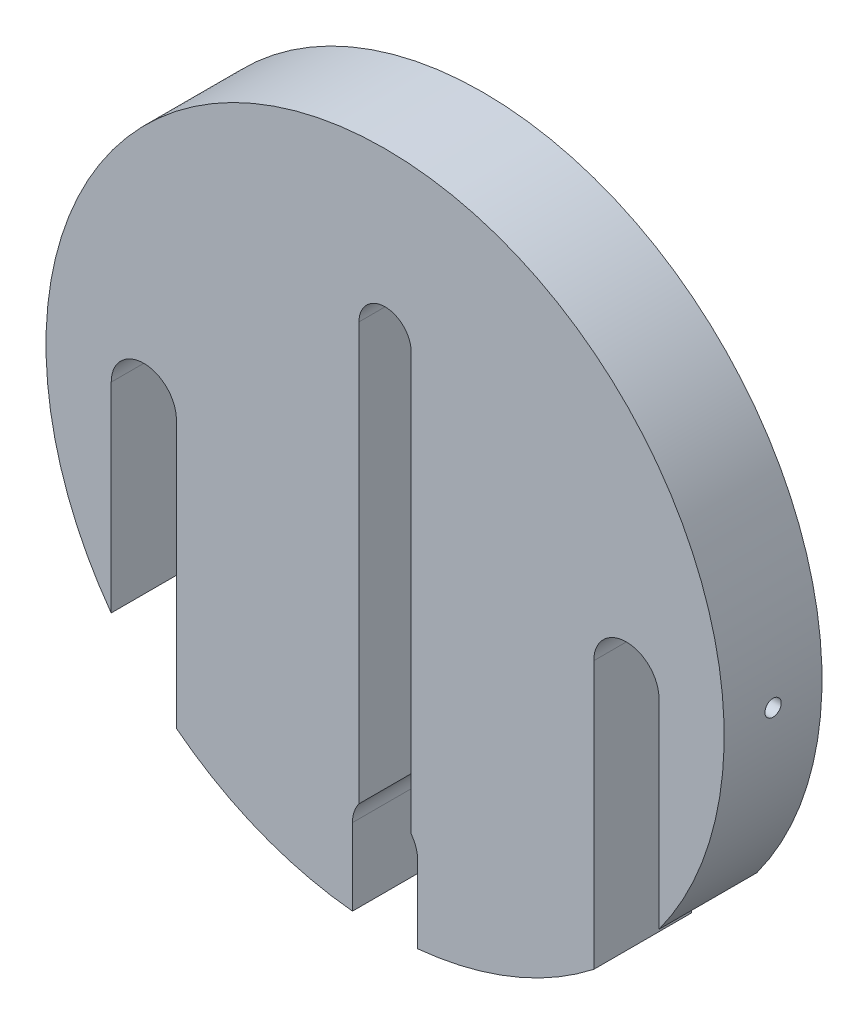
SolidWorks part; units mm, degrees
material "Malleable Cast Iron"
ref_plane "Front Plane" through (0, 0, 0) normal (0, 0, 1) x (1, 0, 0)
ref_plane "Top Plane" through (0, 0, 0) normal (0, 1, 0) x (1, 0, 0)
ref_plane "Right Plane" through (0, 0, 0) normal (1, 0, 0) x (0, 0, -1)
sketch "Sketch1" plane through (0, 0, 0) normal (0, 0, 1) x (1, 0, 0)
  circle A0 centre (0, 0) radius 52
  dimension "D1" = 104
extrude "Boss-Extrude1" add sketch "Sketch1" along normal blind 15
sketch "Sketch2" plane through (0, 0, 15) normal (0, 0, 1) x (1, 0, 0)
  line L0 (0, 0) -> (0, -16.5156) construction
  line L2 (32, 0) -> (32, -45)
  line L3 (32, -45) -> (42, -45)
  line L4 (42, 0) -> (42, -45)
  line L6 (-5, -40) -> (-5, -55)
  line L7 (-5, -55) -> (5, -55)
  line L8 (5, -40) -> (5, -55)
  line L9 (-32, -45) -> (-42, -45)
  line L10 (-42, 0) -> (-42, -45)
  line L12 (-32, 0) -> (-32, -45)
  arc A1 (32, 0) -> (42, 0) centre (37, 0) cw
  arc A2 (-32, 0) -> (-42, 0) centre (-37, 0) ccw
  arc A3 (5, -40) -> (-5, -40) centre (0, -40) ccw
  dimension "D9" = 5
  dimension "D3" = 5
  dimension "D2" = 5
extrude "Cut-Extrude1" cut sketch "Sketch2" against normal blind 15
sketch "Sketch3" plane through (0, 0, 15) normal (0, 0, 1) x (1, 0, 0)
  line L2 (4, 27) -> (4, -40)
  line L3 (4, -40) -> (-4, -40)
  line L4 (-4, 27) -> (-4, -40)
  arc A0 (5, -40) -> (-5, -40) centre (0, -40) ccw construction
  arc A2 (-4, 27) -> (4, 27) centre (0, 27) cw
  dimension "D6" = 4
  dimension "D3" = 0
extrude "Cut-Extrude2" cut sketch "Sketch3" against normal blind 30 contours L4 L3 L2 A2
ref_plane "Plane1" through (-52, 0, 0) normal (-1, 0, 0) x (0, 0, 1)
hole_wizard "M3 Tapped Hole1" positions "Sketch7" profile "Sketch8" tap size "M3" standard "ISO"
sketch "Sketch7" plane through (-52, 0, 0) normal (-1, 0, 0) x (0, 0, 1)
  point P0 (7.5, 0)
  dimension "D1" = 7.5
sketch "Sketch8" plane through (-52, 0, 7.5) normal (0, 1, 0) x (0, 0, 1)
  line L0 (0, 0) -> (0, 48)
  line L1 (0, 48) -> (1.25, 48)
  line L2 (1.25, 48) -> (1.25, 0)
  line L5 (1.25, 0) -> (0, 0)
  line L11 (0, -6.35) -> (0, 107.95) construction
  dimension "Thru Tap Drill Dia." = 2.5
  dimension "Thru Tap Drill Depth" = 48
cosmetic thread "Hole Thread2" parameters "D2"=3
mirror "Mirror1" about plane through (0, 0, 0) normal (1, 0, 0) of "M3 Tapped Hole1"
